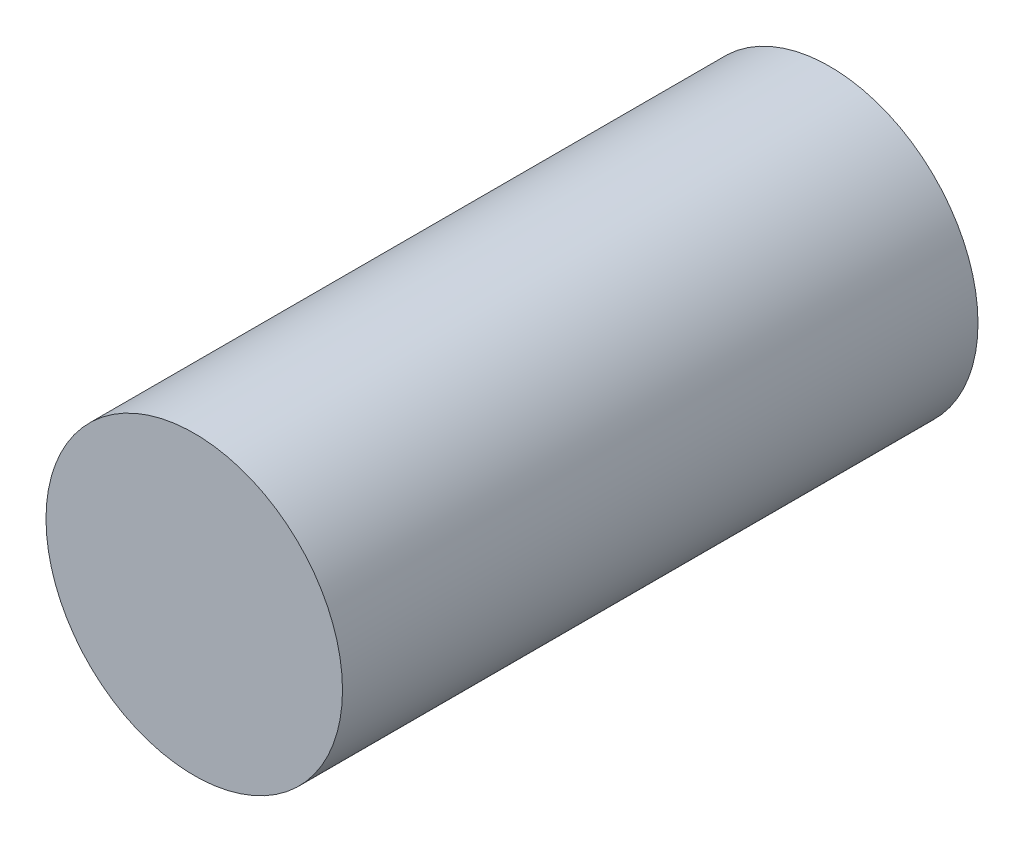
SolidWorks part; units mm, degrees
ref_plane "Front Plane" through (0, 0, 0) normal (0, 0, 1) x (1, 0, 0)
ref_plane "Top Plane" through (0, 0, 0) normal (0, 1, 0) x (1, 0, 0)
ref_plane "Right Plane" through (0, 0, 0) normal (1, 0, 0) x (0, 0, -1)
sketch "Sketch1" plane through (0, 0, 0) normal (0, 0, 1) x (1, 0, 0)
  circle A0 centre (0, 0) radius 38.1
  dimension "D1" = 76.2
extrude "Boss-Extrude1" add sketch "Sketch1" along normal blind 163.322
